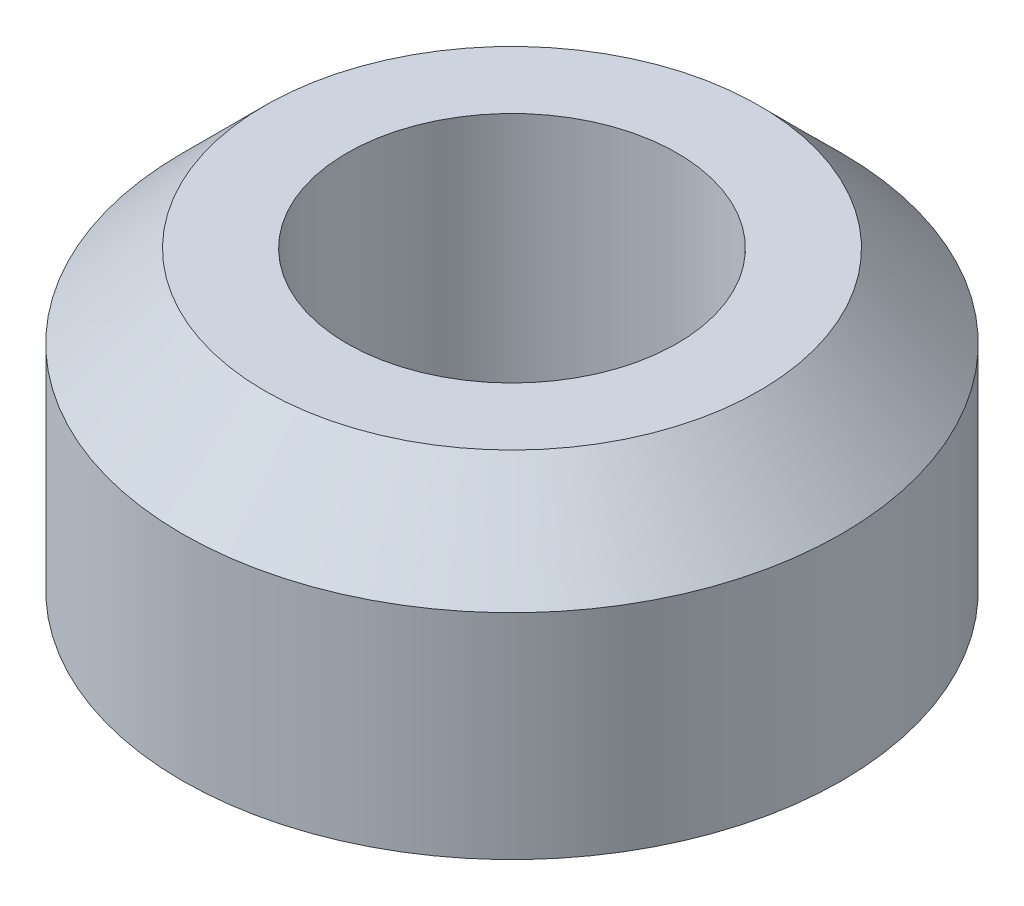
SolidWorks part; units mm, degrees
ref_plane "Front Plane" through (0, 0, 0) normal (0, 0, 1) x (1, 0, 0)
ref_plane "Top Plane" through (0, 0, 0) normal (0, 1, 0) x (1, 0, 0)
ref_plane "Right Plane" through (0, 0, 0) normal (1, 0, 0) x (0, 0, -1)
sketch "Sketch1" plane through (0, 0, 0) normal (0, 0, 1) x (1, 0, 0)
  line L0 (3.175, 0.325) -> (6.3417, 0.325)
  line L1 (6.3417, 0.325) -> (6.3417, 4.4375)
  line L2 (6.3417, 4.4375) -> (4.7542, 6.025)
  line L3 (4.7542, 6.025) -> (3.175, 6.025)
  line L4 (0, 6.35) -> (0, 0) construction
  line L5 (0, 3.175) -> (3.175, 3.175) construction
  line L6 (3.175, 0.325) -> (3.175, 6.025) construction
  line L7 (3.175, 0.325) -> (3.175, 6.025)
  point P11 (3.175, 3.175)
  point P12 (3.175, 3.175)
  dimension "D1" = 1.5875
  dimension "D2" = 1.5875
  dimension "D3" = 5.7
  dimension "D4" = 6.35
  dimension "D5" = 6.35
  dimension "D6" = 3.175
revolve "Revolve1" add sketch "Sketch1" angle 360 about L4
